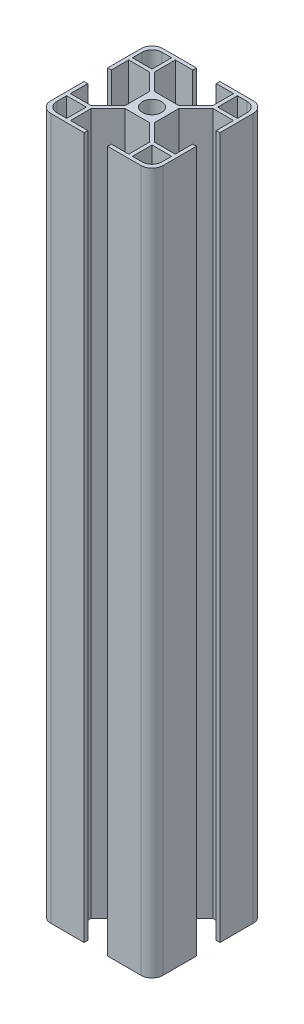
SolidWorks part; units mm, degrees
ref_plane "前视基准面" through (0, 0, 0) normal (0, 0, 1) x (1, 0, 0)
ref_plane "上视基准面" through (0, 0, 0) normal (0, 1, 0) x (1, 0, 0)
ref_plane "右视基准面" through (0, 0, 0) normal (1, 0, 0) x (0, 0, -1)
sketch "草图1" plane through (0, 0, 0) normal (0, 1, 0) x (1, 0, 0)
  line L0 (0, 0) -> (-20, 0) construction
  line L1 (-16.0792, 20) -> (16.0792, 20)
  line L2 (-20, 16.0792) -> (-20, -16.0792)
  line L3 (-16.0792, -20) -> (16.0792, -20)
  line L4 (20, 16.0792) -> (20, -16.0792)
  line L5 (-20, 20) -> (20, -20) construction
  line L6 (-20, -20) -> (20, 20) construction
  line L7 (-5.25, 5.25) -> (5.25, 5.25)
  line L8 (-5.25, 5.25) -> (-5.25, -5.25)
  line L9 (-5.25, -5.25) -> (5.25, -5.25)
  line L10 (5.25, 5.25) -> (5.25, -5.25)
  line L11 (-5.25, 5.25) -> (5.25, -5.25) construction
  line L12 (-5.25, -5.25) -> (5.25, 5.25) construction
  line L17 (-20.658, 20.658) -> (-10.3955, 10.3955) construction
  line L18 (-10.4, 11.3192) -> (-4.3308, 5.25)
  line L19 (-20, 20) -> (-10.4, 20)
  line L20 (-20, 20) -> (-20, 10.4)
  line L21 (-20, 10.4) -> (-10.4, 10.4)
  line L22 (-10.4, 20) -> (-10.4, 10.4)
  line L23 (-20, 20) -> (-10.4, 10.4) construction
  line L24 (-20, 10.4) -> (-10.4, 20) construction
  line L25 (-11.3192, 10.4) -> (-5.25, 4.3308)
  line L26 (-18.7, -11.7) -> (-18.7, -18.7)
  line L27 (-18.7, 11.7) -> (-11.7, 11.7)
  line L28 (-18.7, 11.7) -> (-18.7, 18.7)
  line L29 (-18.7, 18.7) -> (-11.7, 18.7)
  line L30 (-11.7, 11.7) -> (-11.7, 18.7)
  line L31 (-18.7, 11.7) -> (-11.7, 18.7) construction
  line L32 (-18.7, 18.7) -> (-11.7, 11.7) construction
  line L33 (-20, 10.4) -> (-18.7, 10.4)
  line L34 (-20, 10.4) -> (-20, 4.2)
  line L35 (-20, 4.2) -> (-18.7, 4.2)
  line L36 (-18.7, 10.4) -> (-18.7, 4.2)
  line L37 (-18.7, -18.7) -> (-11.7, -18.7)
  line L38 (-11.7, -11.7) -> (-11.7, -18.7)
  line L39 (-18.7, -11.7) -> (-11.7, -11.7)
  line L40 (-20, -4.2) -> (-18.7, -4.2)
  line L41 (-18.7, -10.4) -> (-18.7, -4.2)
  line L42 (-10.4, -11.3192) -> (-4.3308, -5.25)
  line L43 (-11.3192, -10.4) -> (-5.25, -4.3308)
  line L44 (-20, -10.4) -> (-10.4, -10.4)
  line L45 (-10.4, -20) -> (-10.4, -10.4)
  line L46 (0, 20) -> (0, -20) construction
  line L47 (18.7, 18.7) -> (11.7, 18.7)
  line L48 (11.7, 11.7) -> (11.7, 18.7)
  line L49 (18.7, 11.7) -> (11.7, 11.7)
  line L50 (18.7, 11.7) -> (18.7, 18.7)
  line L51 (10.4, 20) -> (10.4, 10.4)
  line L52 (20, 10.4) -> (10.4, 10.4)
  line L53 (20, 4.2) -> (18.7, 4.2)
  line L54 (18.7, 10.4) -> (18.7, 4.2)
  line L55 (10.4, 11.3192) -> (4.3308, 5.25)
  line L56 (11.3192, 10.4) -> (5.25, 4.3308)
  line L57 (11.3192, -10.4) -> (5.25, -4.3308)
  line L58 (10.4, -11.3192) -> (4.3308, -5.25)
  line L59 (18.7, -10.4) -> (18.7, -4.2)
  line L60 (20, -4.2) -> (18.7, -4.2)
  line L61 (20, -10.4) -> (10.4, -10.4)
  line L62 (10.4, -20) -> (10.4, -10.4)
  line L63 (18.7, -11.7) -> (11.7, -11.7)
  line L64 (11.7, -11.7) -> (11.7, -18.7)
  line L65 (18.7, -18.7) -> (11.7, -18.7)
  line L66 (18.7, -11.7) -> (18.7, -18.7)
  line L67 (-4.2, 20) -> (-4.2, 18.7)
  line L68 (-10.4, 18.7) -> (-4.2, 18.7)
  line L69 (-4.2, -20) -> (-4.2, -18.7)
  line L70 (-10.4, -18.7) -> (-4.2, -18.7)
  line L71 (4.2, -20) -> (4.2, -18.7)
  line L72 (10.4, -18.7) -> (4.2, -18.7)
  line L73 (10.4, 18.7) -> (4.2, 18.7)
  line L74 (4.2, 20) -> (4.2, 18.7)
  circle A0 centre (0, 0) radius 3.4
  arc A1 (20, 16.0792) -> (16.0792, 20) centre (16.0792, 16.0792) ccw
  arc A2 (16.0792, -20) -> (20, -16.0792) centre (16.0792, -16.0792) ccw
  arc A3 (-16.0792, -20) -> (-20, -16.0792) centre (-16.0792, -16.0792) cw
  arc A4 (-20, 16.0792) -> (-16.0792, 20) centre (-16.0792, 16.0792) cw
  circle A5 centre (-15.2, 15.2) radius 3.5
  circle A6 centre (-15.2, -15.2) radius 3.5
  circle A7 centre (15.2, 15.2) radius 3.5
  circle A8 centre (15.2, -15.2) radius 3.5
  point P23 (-15.5268, 15.5268)
  point P26 (-15.2, 15.2)
  point P36 (-15.2, 15.2)
  dimension "D1" = 6.8
  dimension "D4" = 3.9208
  dimension "D2" = 40
  dimension "D3" = 40
  dimension "D5" = 14.75
  dimension "D6" = 14.75
  dimension "D7" = 10.4
  dimension "D8" = 0.65
  dimension "D9" = 7
  dimension "D10" = 1.3
  dimension "D11" = 4.2
extrude "凸台-拉伸2" add sketch "草图1" along normal blind 250 contours L70 L45 L3 L69 | A3 L3 L45 L44 L2 L26 L39 L38 L37 | L2 L44 L41 L40 | L37 A6 L26 | L45 L42 L9 L8 L43 L44 | L10 L7 L8 L9 A0 | L58 L62 L61 L57 L10 L9 | L56 L52 L51 L55 L7 L10 | L21 L25 L8 L7 L18 L22 | L3 A2 L4 L61 L62 L63 L66 L65 L64 | A8 L65 L66 | L47 A7 L50 | L4 A1 L1 L51 L52 L50 L49 L48 L47 | A5 L29 L28 | A4 L2 L21 L22 L1 L30 L27 L28 L29 | L22 L68 L67 L1 | L1 L74 L73 L51 | L52 L54 L53 L4 | L36 L21 L2 L35 | L61 L4 L60 L59 | L62 L72 L71 L3
